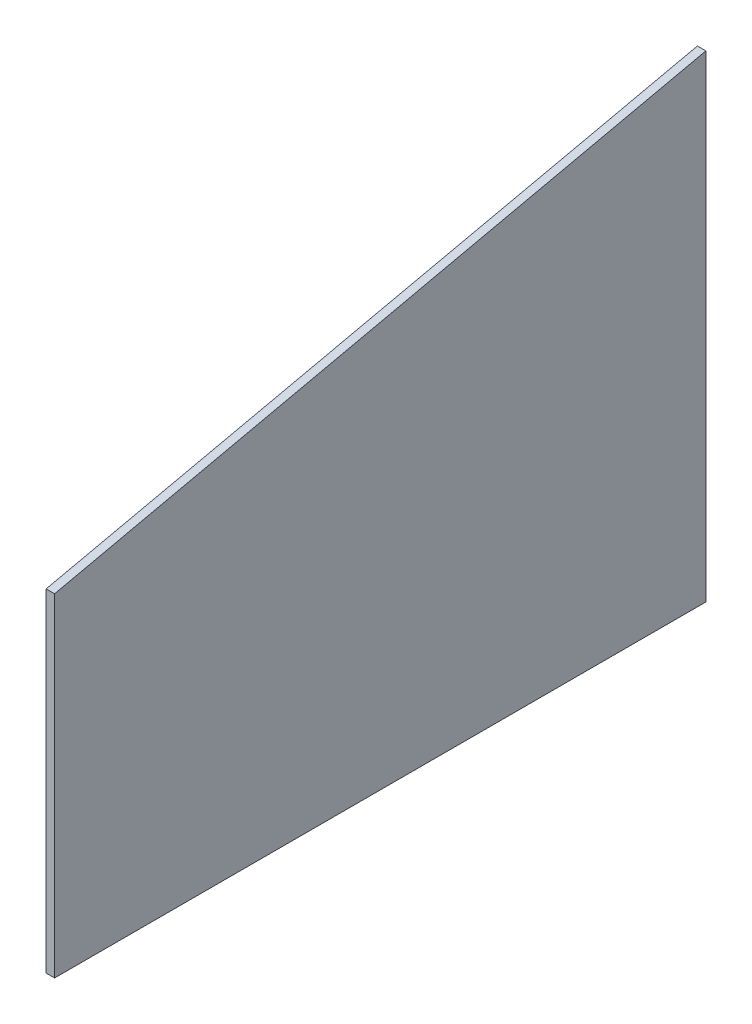
SolidWorks part; units mm, degrees
ref_plane "Front Plane" through (0, 0, 0) normal (0, 0, 1) x (1, 0, 0)
ref_plane "Top Plane" through (0, 0, 0) normal (0, 1, 0) x (1, 0, 0)
ref_plane "Right Plane" through (0, 0, 0) normal (1, 0, 0) x (0, 0, -1)
sketch "Sketch1" plane through (0, 0, 0) normal (1, 0, 0) x (0, 0, -1)
  line L0 (0, 0) -> (196.85, 0)
  line L1 (196.85, 0) -> (196.85, 144.272)
  line L2 (196.85, 144.272) -> (0, 100.584)
  line L3 (0, 100.584) -> (0, 0)
  dimension "D1" = 100.584
  dimension "D2" = 196.85
  dimension "D3" = 144.272
extrude "Boss-Extrude1" add sketch "Sketch1" along normal blind 2.54
